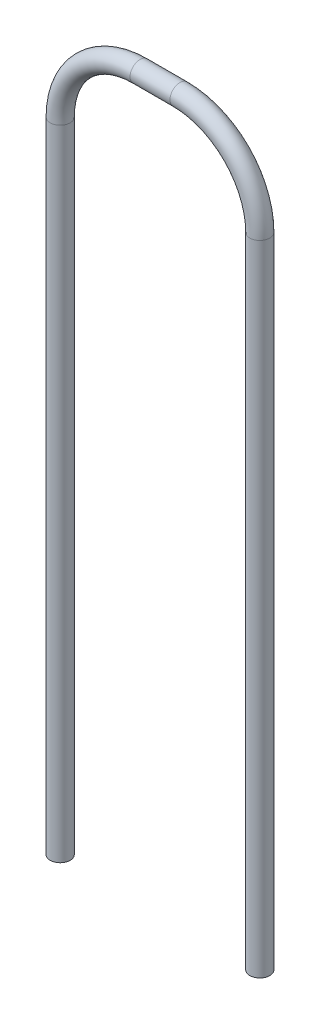
SolidWorks part; units mm, degrees
ref_plane "Front Plane" through (0, 0, 0) normal (0, 0, 1) x (1, 0, 0)
ref_plane "Top Plane" through (0, 0, 0) normal (0, 1, 0) x (1, 0, 0)
ref_plane "Right Plane" through (0, 0, 0) normal (1, 0, 0) x (0, 0, -1)
sketch "Sketch1" plane through (0, 0, 0) normal (0, 1, 0) x (1, 0, 0)
  line L0 (0, 0) -> (-2.5, 0) construction
  circle A1 centre (-2.4994, 0) radius 0.25
  dimension "D1" = 0.5
  dimension "D2" = 2.5
sketch "Sketch2" plane through (0, 0, 0) normal (0, 0, 1) x (1, 0, 0)
  line L0 (-2.4994, 0) -> (-2.4994, 16)
  line L1 (-2.2494, 0) -> (-2.7494, 0) construction
  line L2 (-0.4994, 18) -> (0.5006, 18)
  line L3 (2.5006, 16) -> (2.5006, 0)
  arc A0 (-2.4994, 16) -> (-0.4994, 18) centre (-0.4994, 16) cw
  arc A1 (0.5006, 18) -> (2.5006, 16) centre (0.5006, 16) cw
  point P4 (-2.4994, 18)
  dimension "D1" = 2
  dimension "D2" = 2
sweep "Sweep1" add profiles "Sketch1" path "Sketch2"
